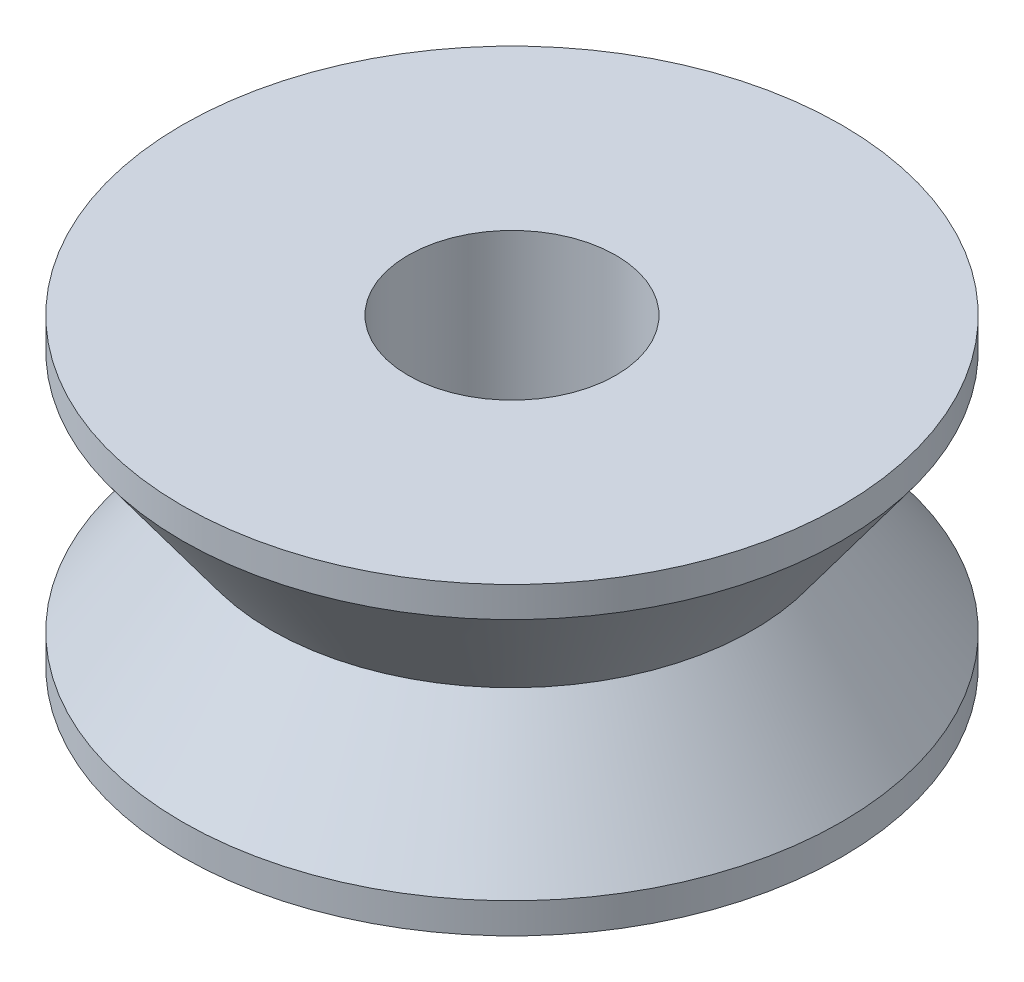
SolidWorks part; units mm, degrees
ref_plane "Front" through (0, 0, 0) normal (0, 0, 1) x (1, 0, 0)
ref_plane "Top" through (0, 0, 0) normal (0, 1, 0) x (1, 0, 0)
ref_plane "Right" through (0, 0, 0) normal (1, 0, 0) x (0, 0, -1)
sketch "Sketch1" plane through (0, 0, 0) normal (0, 0, 1) x (1, 0, 0)
  line L0 (0, 0) -> (0, 6) construction
  line L1 (0, 6) -> (6.5, 6)
  line L2 (6.5, 6) -> (6.5, 5.4)
  line L3 (6.5, 5.4) -> (4.75, 3)
  line L4 (4.75, 3) -> (6.5, 0.6)
  line L5 (6.5, 0.6) -> (6.5, 0)
  line L6 (6.5, 0) -> (0, 0)
  line L7 (0, 0) -> (0, 6)
  dimension "D1" = 6
  dimension "D2" = 13
  dimension "D3" = 9.5
  dimension "D4" = 0.6
revolve "Revolve1" add sketch "Sketch1" angle 360 about L0
sketch "Sketch2" plane through (0, 6, 0) normal (0, 1, 0) x (1, 0, 0)
  circle A0 centre (0, 0) radius 2.05
  dimension "D1" = 4.1
extrude "Cut-Extrude1" cut sketch "Sketch2" against normal up to next
